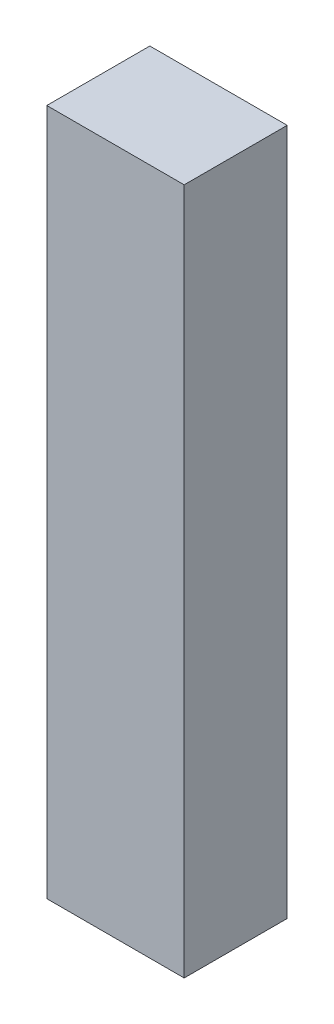
SolidWorks part; units mm, degrees
ref_plane "前基準面" through (0, 0, 0) normal (0, 0, 1) x (1, 0, 0)
ref_plane "上基準面" through (0, 0, 0) normal (0, 1, 0) x (1, 0, 0)
ref_plane "右基準面" through (0, 0, 0) normal (1, 0, 0) x (0, 0, -1)
sketch "草圖1" plane through (0, 0, 0) normal (0, 1, 0) x (1, 0, 0)
  line L1 (-200, 150) -> (200, 150)
  line L2 (-200, 150) -> (-200, -150)
  line L3 (-200, -150) -> (200, -150)
  line L4 (200, 150) -> (200, -150)
  line L5 (-200, 150) -> (200, -150) construction
  line L6 (-200, -150) -> (200, 150) construction
  point P0 (0, 0)
  dimension "D1" = 400
  dimension "D2" = 300
extrude "填料-伸長1" add sketch "草圖1" along normal blind 2000
